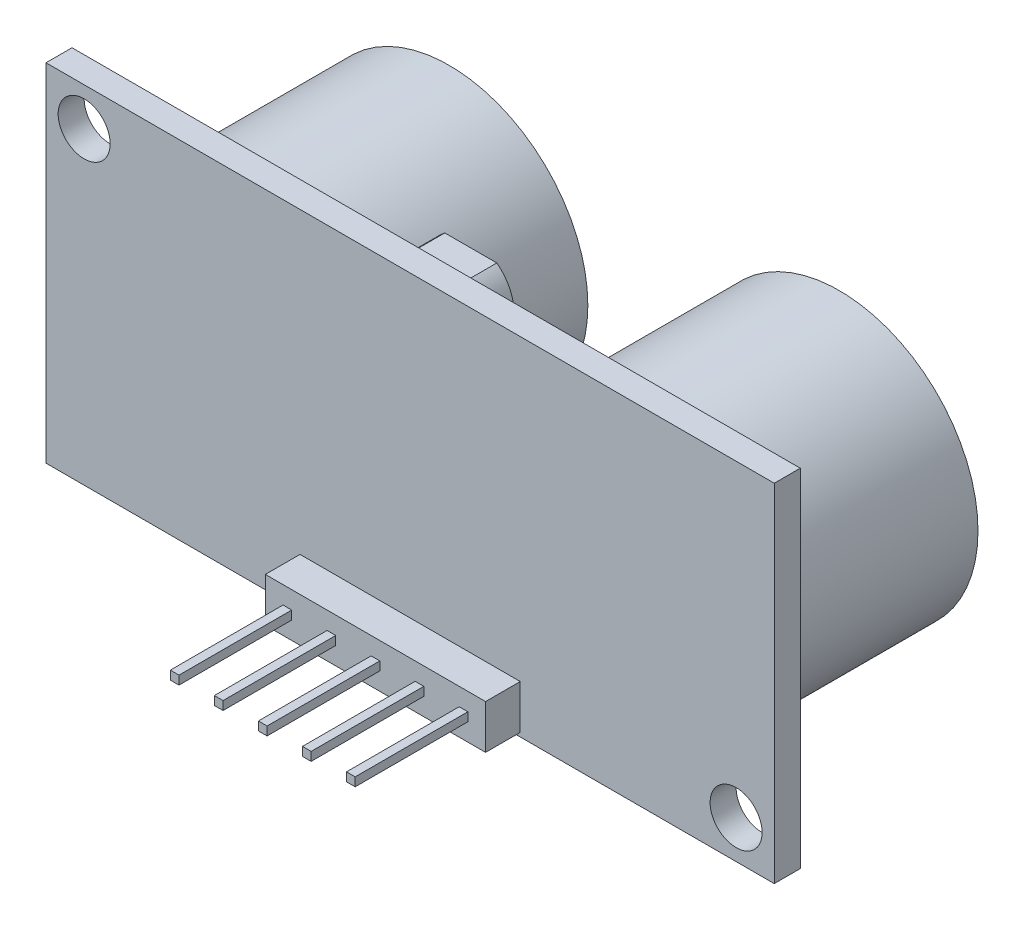
SolidWorks part; units mm, degrees
ref_plane "Alzado" through (0, 0, 0) normal (0, 0, 1) x (1, 0, 0)
ref_plane "Planta" through (0, 0, 0) normal (0, 1, 0) x (1, 0, 0)
ref_plane "Vista lateral" through (0, 0, 0) normal (1, 0, 0) x (0, 0, -1)
sketch "Croquis1" plane through (0, 0, 0) normal (0, 0, 1) x (1, 0, 0)
  line L0 (-18.8, 7.8) -> (0, 0) construction
  line L1 (21, -10) -> (-21, -10)
  line L2 (21, -10) -> (21, 10)
  line L3 (21, 10) -> (-21, 10)
  line L4 (-21, -10) -> (-21, 10)
  line L5 (21, -10) -> (-21, 10) construction
  line L6 (21, 10) -> (-21, -10) construction
  line L7 (0, 0) -> (18.8, -7.8) construction
  circle A0 centre (-18.8, 7.8) radius 1.5
  circle A1 centre (18.8, -7.8) radius 1.5
  point P0 (0, 0)
  dimension "D3" = 3
  dimension "D4" = 3
  dimension "D1" = 20
  dimension "D2" = 42
  dimension "D5" = 37.6
  dimension "D6" = 15.6
extrude "Saliente-Extruir1" add sketch "Croquis1" against normal blind 1.5
sketch "Croquis2" plane through (0, 0, -1.5) normal (0, 0, -1) x (-1, 0, 0)
  line L0 (21, 0) -> (-21, 0) construction
  line L1 (21, 10) -> (21, -10) construction
  line L2 (-21, -10) -> (-21, 10) construction
  line L3 (21, 0) -> (-19.25, 0) construction
  line L4 (21, 0) -> (-19.25, 0) construction
  line L6 (19.25, 0) -> (-21, 0) construction
  circle A0 centre (-11.25, 0) radius 8
  circle A1 centre (11.25, 0) radius 8
  point P10 (-19.25, 0)
  point P11 (19.25, 0)
  dimension "D1" = 16
  dimension "D2" = 38.5
extrude "Saliente-Extruir2" add sketch "Croquis2" along normal blind 12
sketch "Croquis3" plane through (0, 0, -13.5) normal (0, 0, -1) x (-1, 0, 0)
  circle A0 centre (-11.25, 0) radius 6.5
  circle A1 centre (11.25, 0) radius 6.5
  dimension "D1" = 13
extrude "Cortar-Extruir1" cut sketch "Croquis3" against normal blind 0.5
sketch "Croquis4" plane through (0, 0, -1.5) normal (0, 0, -1) x (-1, 0, 0)
  line L0 (0, 0) -> (0, -10) construction
  line L1 (21, -10) -> (-21, -10) construction
  line L2 (0, -8.5) -> (-2.54, -8.5) construction
  line L3 (-2.54, -8.5) -> (-5.08, -8.5) construction
  line L6 (5.08, -8.5) -> (2.54, -8.5) construction
  line L7 (2.54, -8.5) -> (0, -8.5) construction
  dimension "D1" = 2.54
  dimension "D2" = 1.5
sketch "Croquis5" plane through (0, 0, 0) normal (0, 0, 1) x (1, 0, 0)
  line L1 (0.25, -8.25) -> (-0.25, -8.25)
  line L2 (0.25, -8.25) -> (0.25, -8.75)
  line L3 (0.25, -8.75) -> (-0.25, -8.75)
  line L4 (-0.25, -8.25) -> (-0.25, -8.75)
  line L5 (0.25, -8.25) -> (-0.25, -8.75) construction
  line L6 (0.25, -8.75) -> (-0.25, -8.25) construction
  line L7 (-2.29, -8.25) -> (-2.79, -8.25)
  line L8 (-2.29, -8.25) -> (-2.29, -8.75)
  line L9 (-2.29, -8.75) -> (-2.79, -8.75)
  line L10 (-2.79, -8.25) -> (-2.79, -8.75)
  line L11 (-2.29, -8.25) -> (-2.79, -8.75) construction
  line L12 (-2.29, -8.75) -> (-2.79, -8.25) construction
  line L13 (-4.83, -8.25) -> (-5.33, -8.25)
  line L14 (-4.83, -8.25) -> (-4.83, -8.75)
  line L15 (-4.83, -8.75) -> (-5.33, -8.75)
  line L16 (-5.33, -8.25) -> (-5.33, -8.75)
  line L17 (-4.83, -8.25) -> (-5.33, -8.75) construction
  line L18 (-4.83, -8.75) -> (-5.33, -8.25) construction
  line L19 (2.79, -8.25) -> (2.29, -8.25)
  line L20 (2.79, -8.25) -> (2.79, -8.75)
  line L21 (2.79, -8.75) -> (2.29, -8.75)
  line L22 (2.29, -8.25) -> (2.29, -8.75)
  line L23 (2.79, -8.25) -> (2.29, -8.75) construction
  line L24 (2.79, -8.75) -> (2.29, -8.25) construction
  line L25 (5.33, -8.25) -> (4.83, -8.25)
  line L26 (5.33, -8.25) -> (5.33, -8.75)
  line L27 (5.33, -8.75) -> (4.83, -8.75)
  line L28 (4.83, -8.25) -> (4.83, -8.75)
  line L29 (5.33, -8.25) -> (4.83, -8.75) construction
  line L30 (5.33, -8.75) -> (4.83, -8.25) construction
  point P0 (0, -8.5)
  point P6 (-2.54, -8.5)
  point P12 (-5.08, -8.5)
  point P18 (2.54, -8.5)
  point P24 (5.08, -8.5)
  dimension "D1" = 0.5
extrude "Saliente-Extruir3" add sketch "Croquis5" against normal blind 3 and the other way blind 8.5
sketch "Croquis6" plane through (0, 0, 0) normal (0, 0, 1) x (1, 0, 0)
  line L0 (-2.54, -8.5) -> (0, -8.5) construction
  line L1 (6.35, -9.77) -> (-6.35, -9.77)
  line L2 (6.35, -9.77) -> (6.35, -7.23)
  line L3 (6.35, -7.23) -> (-6.35, -7.23)
  line L4 (-6.35, -9.77) -> (-6.35, -7.23)
  line L5 (6.35, -9.77) -> (-6.35, -7.23) construction
  line L6 (6.35, -7.23) -> (-6.35, -9.77) construction
  point P0 (0, -8.5)
  dimension "D1" = 12.7
  dimension "D2" = 2.54
extrude "Saliente-Extruir4" add sketch "Croquis6" along normal blind 2
sketch "Croquis7" plane through (0, 0, -1.5) normal (0, 0, -1) x (-1, 0, 0)
  line L0 (-2.5, -7) -> (0, -7)
  line L1 (0, -7) -> (2.5, -7)
  line L2 (0, 0) -> (0, -10) construction
  arc A0 (-2.5, -7) -> (2.5, -7) centre (0, -7) cw
  dimension "D1" = 5
  dimension "D2" = 3
extrude "Saliente-Extruir5" add sketch "Croquis7" along normal blind 4
sketch "Croquis8" plane through (0, 0, -1.5) normal (0, 0, -1) x (-1, 0, 0)
  line L0 (0, 0) -> (0, 10) construction
  line L1 (-21, 10) -> (21, 10) construction
  line L3 (-1.5, 9.5) -> (1.5, 9.5)
  line L5 (-1.5, 5.5) -> (1.5, 5.5)
  line L7 (-1.5, 9.5) -> (1.5, 5.5) construction
  line L8 (-1.5, 5.5) -> (1.5, 9.5) construction
  arc A0 (1.5, 5.5) -> (1.5, 9.5) centre (0, 7.5) ccw
  arc A1 (-1.5, 9.5) -> (-1.5, 5.5) centre (0, 7.5) ccw
  dimension "D1" = 5
  dimension "D2" = 3
extrude "Saliente-Extruir6" add sketch "Croquis8" along normal blind 2
